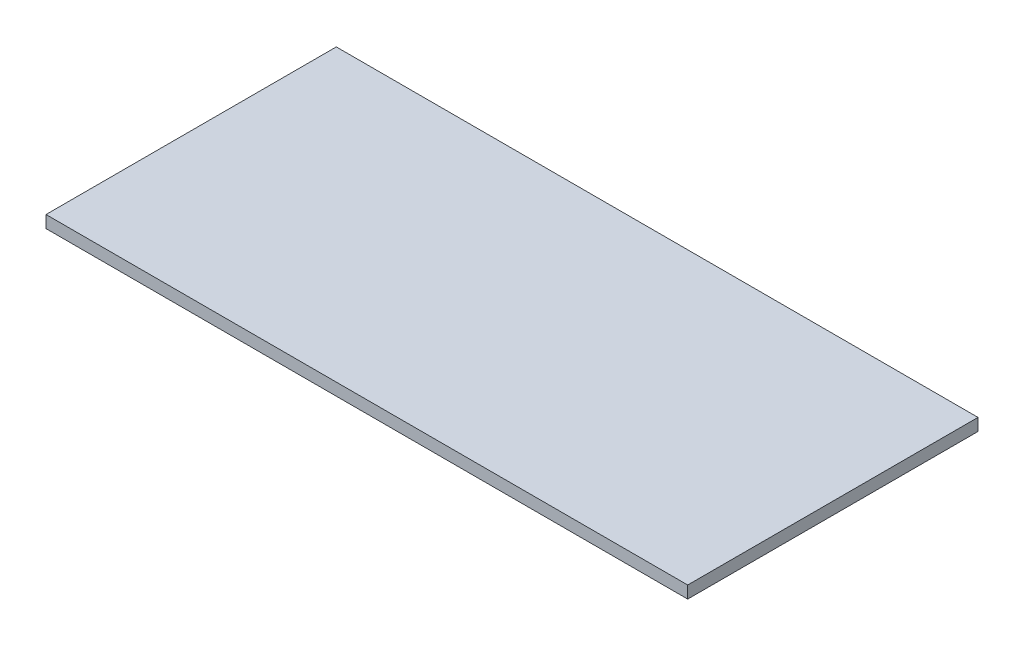
SolidWorks part; units mm, degrees
ref_plane "Front Plane" through (0, 0, 0) normal (0, 0, 1) x (1, 0, 0)
ref_plane "Top Plane" through (0, 0, 0) normal (0, 1, 0) x (1, 0, 0)
ref_plane "Right Plane" through (0, 0, 0) normal (1, 0, 0) x (0, 0, -1)
sketch "Sketch1" plane through (0, 0, 0) normal (0, 1, 0) x (1, 0, 0)
  line L1 (-105, -47.5) -> (105, -47.5)
  line L2 (-105, -47.5) -> (-105, 47.5)
  line L3 (-105, 47.5) -> (105, 47.5)
  line L4 (105, -47.5) -> (105, 47.5)
  line L5 (-105, -47.5) -> (105, 47.5) construction
  line L6 (-105, 47.5) -> (105, -47.5) construction
  point P0 (0, 0)
  dimension "D1" = 210
  dimension "D2" = 95
extrude "Boss-Extrude1" add sketch "Sketch1" along normal blind 4
